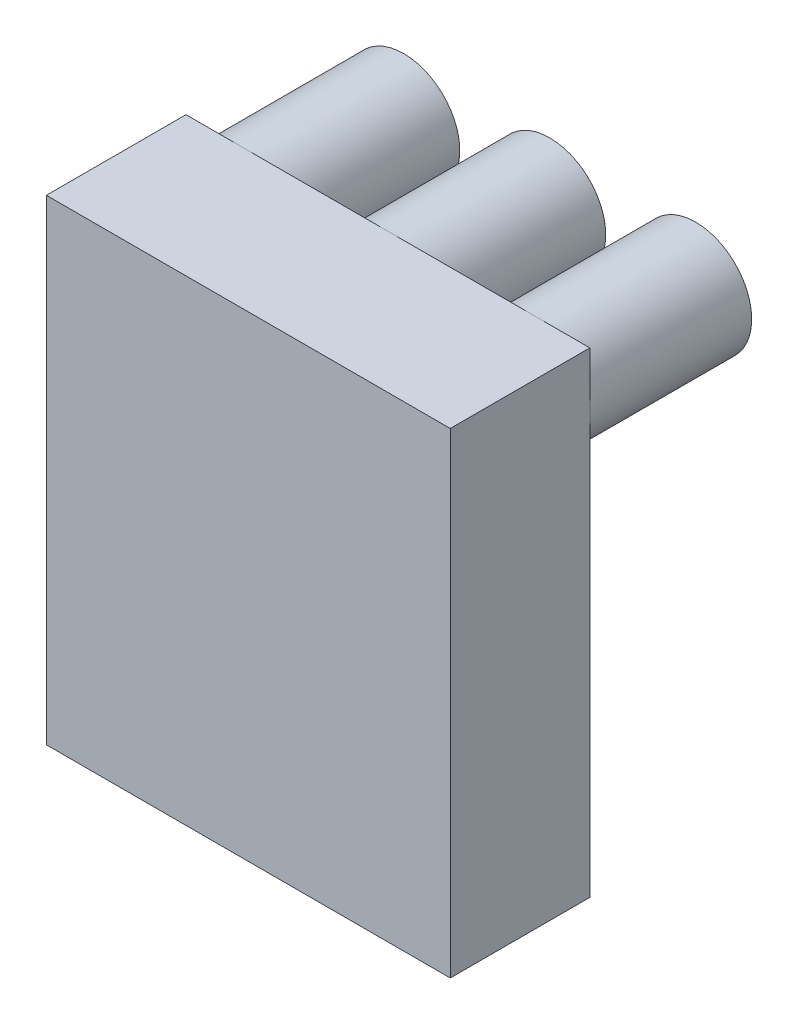
SolidWorks part; units mm, degrees
ref_plane "Front Plane" through (0, 0, 0) normal (0, 0, 1) x (1, 0, 0)
ref_plane "Top Plane" through (0, 0, 0) normal (0, 1, 0) x (1, 0, 0)
ref_plane "Right Plane" through (0, 0, 0) normal (1, 0, 0) x (0, 0, -1)
sketch "Sketch1" plane through (0, 0, 0) normal (0, 0, 1) x (1, 0, 0)
  line L0 (-1.7145, -11.0758) -> (-1.7145, -12.1045)
  line L1 (-1.7145, -12.1045) -> (1.7145, -12.1045)
  line L2 (1.7145, -12.1045) -> (1.7145, -11.0758)
  circle A0 centre (0, 0) radius 11.2077
  point P6 (0, -12.1045)
  dimension "D1" = 22.4155
  dimension "D2" = 1.0287
  dimension "D3" = 3.429
extrude "Boss-Extrude1" add sketch "Sketch1" along normal blind 60.325 contours A0 | A0 L0 L1 L2
pattern_linear "LPattern1" count 2 spacing 29.21 along (1, 0, 0) count 2 spacing 29.21 along (-1, 0, 0) of "Boss-Extrude1"
sketch "Sketch2" plane through (0, 0, 0) normal (0, 1, 0) x (1, 0, 0)
  line L0 (-40.4177, 0) -> (-40.4177, -60.325) construction
  line L1 (40.4177, -60.325) -> (-40.4177, -60.325)
  line L2 (40.4177, -60.325) -> (40.4177, -32.385)
  line L3 (40.4177, -32.385) -> (-40.4177, -32.385)
  line L4 (-40.4177, -60.325) -> (-40.4177, -32.385)
  line L5 (18.0022, -60.325) -> (40.4177, -60.325) construction
  dimension "D1" = 27.94
extrude "Boss-Extrude2" add sketch "Sketch2" along normal up to vertex (11.2078 mm away) and the other way blind 84.0422
